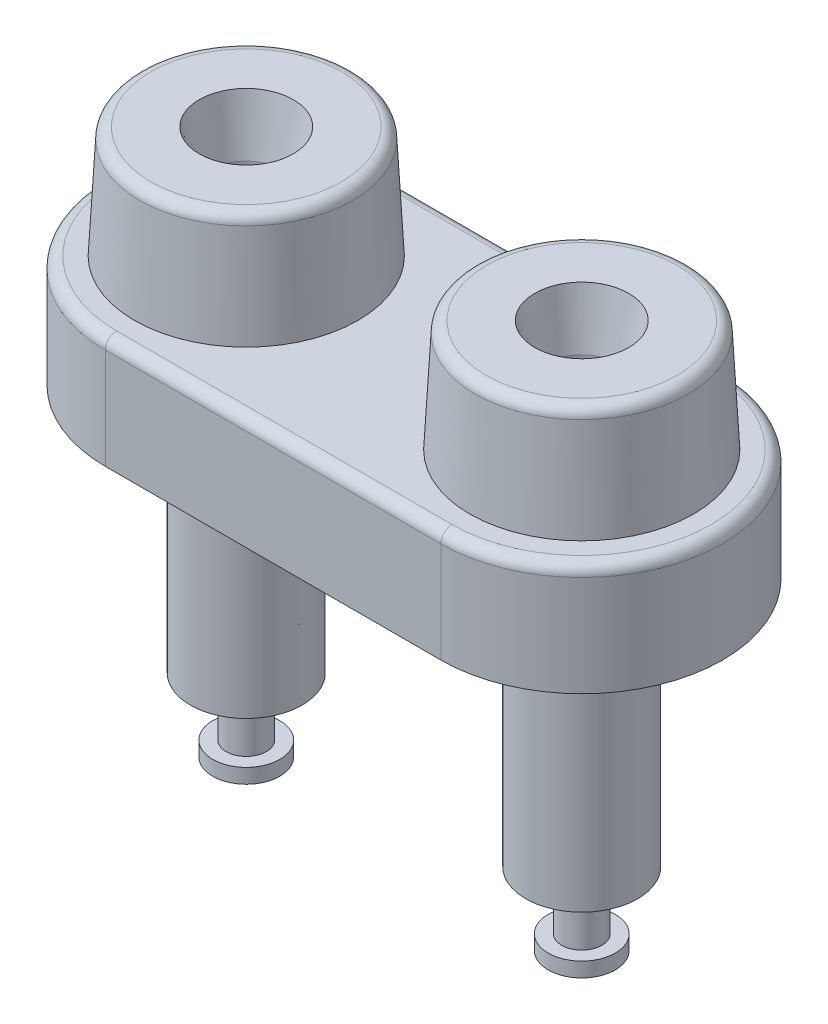
SolidWorks part; units mm, degrees
ref_plane "Front Plane" through (0, 0, 0) normal (0, 0, 1) x (1, 0, 0)
ref_plane "Top Plane" through (0, 0, 0) normal (0, 1, 0) x (1, 0, 0)
ref_plane "Right Plane" through (0, 0, 0) normal (1, 0, 0) x (0, 0, -1)
ref_plane "Plane1" through (0, 6.35, 0) normal (0, 1, 0) x (1, 0, 0)
ref_plane "Plane2" through (0, -4.75, 0) normal (0, 1, 0) x (1, 0, 0)
sketch "Sketch1" plane through (0, 0, 0) normal (0, 1, 0) x (1, 0, 0)
  line L0 (-9.525, 0) -> (9.525, 0) construction
  line L1 (-9.525, 8.001) -> (9.525, 8.001)
  line L2 (-9.525, -8.001) -> (9.525, -8.001)
  arc A0 (-9.525, 8.001) -> (-9.525, -8.001) centre (-9.525, 0) ccw
  arc A1 (9.525, -8.001) -> (9.525, 8.001) centre (9.525, 0) ccw
  point P2 (0, 0)
  dimension "D2" = 8.001
  dimension "D1" = 19.05
extrude "Boss-Extrude1" add sketch "Sketch1" along normal blind 6.35
sketch "Sketch2" plane through (0, 6.35, 0) normal (0, 1, 0) x (1, 0, 0)
  line L0 (0, 0) -> (0, 12.4012) construction
  circle A0 centre (-9.525, 0) radius 6.35
  circle A1 centre (9.525, 0) radius 6.35
  dimension "D1" = 12.7
extrude "Boss-Extrude2" add sketch "Sketch2" along normal blind 6.35 draft 3
sketch "Sketch3" plane through (0, 0, 0) normal (0, -1, 0) x (1, 0, 0)
  circle A0 centre (-9.525, 0) radius 4.699
  circle A1 centre (9.525, 0) radius 4.699
  dimension "D1" = 9.398
extrude "Boss-Extrude3" add sketch "Sketch3" along normal blind 0.889
ref_axis "Axis1" through (9.525, -0.889, 0) along (0, 1, 0)
sketch "Sketch4" plane through (0, 0, 0) normal (0, 0, 1) x (1, 0, 0)
  line L0 (9.525, -0.889) -> (9.525, -18.288)
  line L1 (9.525, -0.889) -> (9.525, 0) construction
  line L2 (9.525, -18.288) -> (7.62, -18.288)
  line L3 (7.62, -18.288) -> (7.62, -17.4569)
  line L4 (7.62, -17.4569) -> (8.382, -17.4569)
  line L5 (8.382, -17.4569) -> (8.382, -14.1549)
  line L6 (8.382, -14.1549) -> (6.35, -14.1549)
  line L7 (6.35, -14.1549) -> (6.35, -0.889)
  line L8 (4.826, -0.889) -> (14.224, -0.889) construction
  line L9 (6.35, -0.889) -> (9.525, -0.889)
  line L10 (15.5422, 12.7) -> (3.5078, 12.7) construction
  dimension "D1" = 3.175
  dimension "D2" = 30.988
  dimension "D3" = 3.302
  dimension "D4" = 1.905
  dimension "D5" = 1.143
revolve "Revolve1" add sketch "Sketch4" angle 360 about axis through (9.525, -0.889, 0) along (0, 1, 0)
pattern_linear "LPattern1" count 2 spacing 19.05 along (-1, 0, 0) of "Revolve1"
fillet "Fillet1" radius 0.635 6 edges at (9.525, 12.7, -6.0172) (-9.525, 12.7, 6.0172) (0, 6.35, -8.001) (17.526, 6.35, 0) (0, 6.35, 8.001) (-17.526, 6.35, 0)
sketch "Sketch5" plane through (0, 12.7, 0) normal (0, 1, 0) x (1, 0, 0)
  circle A0 centre (-9.525, 0) radius 2.1082
  circle A1 centre (9.525, 0) radius 2.1082
  dimension "D1" = 4.2164
extrude "Cut-Extrude1" cut sketch "Sketch5" against normal blind 25.4
ref_axis "Axis2" through (9.525, -12.7, 0) along (0, 1, 0)
sketch "Sketch6" plane through (0, 0, 0) normal (0, 0, 1) x (1, 0, 0)
  line L0 (6.4091, 15.24) -> (7.4168, 9.525)
  line L1 (7.4168, 12.7) -> (7.4168, -12.7) construction
  line L2 (6.4091, 15.24) -> (8.4245, 15.24)
  line L3 (8.4245, 15.24) -> (7.4168, 9.525)
  line L4 (9.525, -12.7) -> (9.525, 12.7) construction
  line L5 (14.9396, 12.7) -> (4.1104, 12.7) construction
  dimension "D1" = 10
  dimension "D2" = 20
  dimension "D3" = 3.175
  dimension "D4" = 2.54
revolve "flare" cut sketch "Sketch6" angle 360 about axis through (9.525, -12.7, 0) along (0, 1, 0)
mirror "Mirror1" about plane through (0, 0, 0) normal (1, 0, 0) of "flare"
